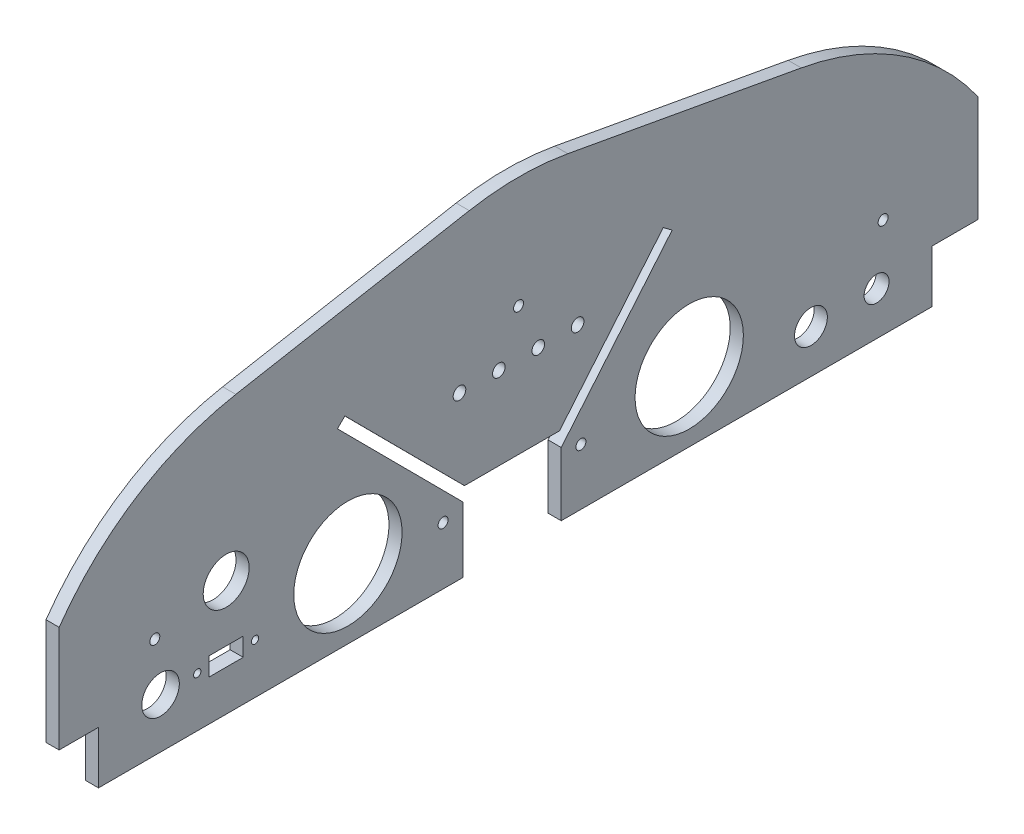
SolidWorks part; units mm, degrees
material "Maple"
ref_plane "Front Plane" through (0, 0, 0) normal (0, 0, 1) x (1, 0, 0)
ref_plane "Top Plane" through (0, 0, 0) normal (0, 1, 0) x (1, 0, 0)
ref_plane "Right Plane" through (0, 0, 0) normal (1, 0, 0) x (0, 0, -1)
sketch "Sketch1" plane through (0, 0, 0) normal (1, 0, 0) x (0, 0, -1)
  line L0 (241.201, 0) -> (185.8087, 79.3068) construction
  line L1 (241.201, 0) -> (-241.201, 0) construction
  line L2 (128.8185, 115.8696) -> (15.8924, 136.3875) construction
  line L3 (241.201, 0) -> (190.401, 0) construction
  line L4 (-15.8924, 136.3875) -> (-128.8185, 115.8696) construction
  line L5 (200.025, 53.34) -> (222.25, 53.34)
  line L6 (-185.8087, 79.3068) -> (-241.201, 0) construction
  line L7 (-241.201, 0) -> (-190.401, 0) construction
  line L8 (136.7647, 159.6035) -> (23.8385, 180.1215)
  line L9 (-137.7917, 27.94) -> (137.7917, 27.94) construction
  line L10 (-23.8385, 180.1215) -> (-136.7647, 159.6035)
  line L11 (-203.2, 53.34) -> (-222.25, 53.34)
  line L12 (222.25, 53.34) -> (222.25, 104.7594)
  line L13 (-222.25, 53.34) -> (-222.25, 104.7594)
  line L15 (200.025, 53.34) -> (200.025, 27.94)
  line L16 (200.025, 27.94) -> (-203.2, 27.94)
  line L17 (-203.2, 27.94) -> (-203.2, 53.34)
  line L18 (171.1515, 182.2695) -> (-131.8993, 182.2695) construction
  line L19 (277.6423, 25.4526) -> (222.25, 104.7594) construction
  line L20 (-222.25, 104.7594) -> (-277.6423, 25.4526) construction
  arc A0 (185.8087, 79.3068) -> (128.8185, 115.8696) centre (112.9261, 28.4016) ccw construction
  arc A1 (15.8924, 136.3875) -> (-15.8924, 136.3875) centre (0, 48.9195) ccw construction
  arc A2 (-128.8185, 115.8696) -> (-185.8087, 79.3068) centre (-112.9261, 28.4016) ccw construction
  arc A3 (-190.401, 0) -> (-137.7917, 27.94) centre (-137.7917, -35.56) cw construction
  arc A4 (137.7917, 27.94) -> (190.401, 0) centre (137.7917, -35.56) cw construction
  arc A5 (222.25, 104.7594) -> (136.7647, 159.6035) centre (112.9261, 28.4016) ccw
  arc A6 (23.8385, 180.1215) -> (-23.8385, 180.1215) centre (0, 48.9195) ccw
  arc A7 (-136.7647, 159.6035) -> (-222.25, 104.7594) centre (-112.9261, 28.4016) ccw
  point P22 (0, 27.94)
  dimension "D1" = 88.9
  dimension "D2" = 88.9
  dimension "D3" = 137.8195
  dimension "D8" = 63.5
  dimension "D4" = 114.775
  dimension "D5" = 114.775
  dimension "D6" = 257.637
  dimension "D7" = 444.5
  dimension "D9" = 27.94
  dimension "D10" = 50.8
  dimension "D12" = 25.4
  dimension "D13" = 19.05
  dimension "D14" = 22.225
  dimension "D11" = 44.45
extrude "Base" add sketch "Sketch1" along normal blind 6.35
sketch "Car Dimensions" plane through (0, 0, 0) normal (1, 0, 0) x (0, 0, -1)
  line L0 (-258.164, 20.0716) -> (-206.6323, 93.8512)
  line L2 (-133.3592, 140.8604) -> (-22.7034, 160.9658)
  line L4 (22.7034, 160.9658) -> (133.3592, 140.8604)
  line L6 (206.6323, 93.8512) -> (259.779, 17.7594)
  line L10 (228.7968, 17.7594) -> (185.8087, 79.3068)
  line L11 (131.0888, 128.365) -> (18.1627, 148.8829)
  line L13 (128.8185, 115.8696) -> (15.8924, 136.3875)
  line L14 (-18.1627, 148.8829) -> (-131.0888, 128.365)
  line L15 (-15.8924, 136.3875) -> (-128.8185, 115.8696)
  line L16 (196.2205, 86.579) -> (248.3531, 11.9391)
  line L17 (-185.8087, 79.3068) -> (-227.1819, 20.0716)
  line L18 (-196.2205, 86.579) -> (-238.3224, 26.3004)
  line L21 (-203.2, 53.34) -> (-203.2, 27.94)
  line L22 (200.025, 53.34) -> (222.25, 53.34)
  line L23 (222.25, 53.34) -> (222.25, 104.7594)
  line L24 (136.7647, 159.6035) -> (23.8385, 180.1215)
  line L25 (-23.8385, 180.1215) -> (-136.7647, 159.6035)
  line L26 (-222.25, 104.7594) -> (-222.25, 53.34)
  line L27 (-222.25, 53.34) -> (-203.2, 53.34)
  line L28 (-203.2, 53.34) -> (-203.2, 27.94)
  line L29 (-203.2, 27.94) -> (200.025, 27.94)
  line L30 (-203.2, 27.94) -> (200.025, 27.94)
  line L31 (136.7647, 159.6035) -> (23.8385, 180.1215)
  line L32 (-23.8385, 180.1215) -> (-136.7647, 159.6035)
  line L33 (200.025, 27.94) -> (200.025, 53.34)
  line L34 (200.025, 27.94) -> (200.025, 53.34)
  arc A0 (-206.6323, 93.8512) -> (-133.3592, 140.8604) centre (-112.9261, 28.4016) cw
  arc A1 (-22.7034, 160.9658) -> (22.7034, 160.9658) centre (0, 36.0116) cw
  arc A2 (133.3592, 140.8604) -> (206.6323, 93.8512) centre (112.9261, 28.4016) cw
  circle A6 centre (0, 36.0116) radius 127
  arc A7 (185.8087, 79.3068) -> (128.8185, 115.8696) centre (112.9261, 28.4016) ccw
  arc A8 (15.8924, 136.3875) -> (-15.8924, 136.3875) centre (0, 48.9195) ccw
  arc A9 (-128.8185, 115.8696) -> (-185.8087, 79.3068) centre (-112.9261, 28.4016) ccw
  arc A12 (196.2205, 86.579) -> (131.0888, 128.365) centre (112.9261, 28.4016) ccw
  arc A13 (18.1627, 148.8829) -> (-18.1627, 148.8829) centre (0, 48.9195) ccw
  arc A14 (-131.0888, 128.365) -> (-196.2205, 86.579) centre (-112.9261, 28.4016) ccw
  arc A17 (222.25, 104.7594) -> (136.7647, 159.6035) centre (112.9261, 28.4016) ccw
  arc A18 (23.8385, 180.1215) -> (-23.8385, 180.1215) centre (0, 48.9195) ccw
  arc A19 (-136.7647, 159.6035) -> (-222.25, 104.7594) centre (-112.9261, 28.4016) ccw
  arc A22 (222.25, 104.7594) -> (136.7647, 159.6035) centre (112.9261, 28.4016) ccw
  arc A23 (23.8385, 180.1215) -> (-23.8385, 180.1215) centre (0, 48.9195) ccw
  arc A24 (-136.7647, 159.6035) -> (-222.25, 104.7594) centre (-112.9261, 28.4016) ccw
  dimension "D2" = 254
  dimension "D3" = 12.7
  dimension "D1" = 12.7
  dimension "D4" = 0
  dimension "D5" = 31.75
sketch "Sketch5" plane through (0, 0, 0) normal (-1, 0, 0) x (0, 0, 1)
  line L0 (-17.4625, 27.94) -> (20.6375, 27.94) construction
  line L1 (-200.025, 27.94) -> (203.2, 27.94) construction
  line L2 (-17.4625, 27.94) -> (-17.4625, 46.99) construction
  line L3 (20.6375, 27.94) -> (20.6375, 46.99) construction
  line L4 (20.6375, 46.99) -> (95.25, 121.9687) construction
  line L5 (-17.4625, 46.99) -> (-76.2, 125.43) construction
  line L6 (-76.2, 125.43) -> (-68.5757, 131.1392) construction
  line L7 (95.25, 121.9687) -> (88.4983, 128.6874) construction
  line L8 (88.4983, 128.6874) -> (26.1569, 66.04) construction
  line L9 (23.8385, 180.1215) -> (136.7647, 159.6035) construction
  line L10 (-68.5757, 131.1392) -> (-19.828, 66.04) construction
  line L11 (-136.7647, 159.6035) -> (-23.8385, 180.1215) construction
  line L12 (23.8385, 180.1215) -> (136.7647, 159.6035) construction
  line L13 (-19.828, 66.04) -> (26.1569, 66.04) construction
  line L14 (-136.7647, 159.6035) -> (-23.8385, 180.1215) construction
  line L15 (-128.8185, 115.8696) -> (-15.8924, 136.3875) construction
  line L16 (15.8924, 136.3875) -> (128.8185, 115.8696) construction
  line L17 (-511.4071, 240.1453) -> (-231.4071, 240.1453) construction
  line L18 (-19.828, 66.04) -> (-69.9993, 126.1067)
  line L19 (-74.2969, 122.8886) -> (-69.9993, 126.1067)
  line L20 (-74.2969, 122.8886) -> (-20.6375, 58.6458)
  line L21 (-20.6375, 58.6458) -> (-20.6375, 27.94)
  line L22 (26.9875, 27.94) -> (26.9875, 59.6728)
  line L23 (84.0192, 124.1863) -> (87.6201, 120.603)
  line L24 (26.1569, 66.04) -> (84.0192, 124.1863)
  line L25 (87.6201, 120.603) -> (26.9875, 59.6728)
  line L26 (-19.828, 66.04) -> (26.1569, 66.04)
  arc A3 (23.8385, 180.1215) -> (-23.8385, 180.1215) centre (0, 48.9195) ccw construction
  arc A4 (23.8385, 180.1215) -> (-23.8385, 180.1215) centre (0, 48.9195) ccw construction
  arc A5 (15.8924, 136.3875) -> (-15.8924, 136.3875) centre (0, 48.9195) ccw construction
  point P4 (1.5875, 27.94)
  point P22 (0, 137.8195)
  dimension "D8" = 76.2
  dimension "D1" = 38.1
  dimension "D2" = 38.1
  dimension "D3" = 19.05
  dimension "D4" = 44.45
  dimension "D5" = 95.25
  dimension "D6" = 9.525
  dimension "D7" = 3.175
  dimension "D9" = 9.525
  dimension "D10" = 6.35
  dimension "D11" = 3.175
  dimension "D12" = 4.445
  dimension "D13" = 6.35
  dimension "D14" = 4.445
extrude "Steering Slot" cut sketch "Sketch5" against normal up to next
sketch "Sketch6" plane through (0, 0, 0) normal (-1, 0, 0) x (0, 0, 1)
  line L4 (-222.25, 53.34) -> (-222.25, 104.7594) construction
  line L5 (222.25, 53.34) -> (222.25, 104.7594) construction
  circle A0 centre (-82.55, 61.6195) radius 26.1938
  circle A1 centre (82.55, 61.6195) radius 26.1938
  circle A2 centre (-82.55, 61.6195) radius 28.829 construction
  circle A3 centre (82.55, 61.6195) radius 28.829 construction
  arc A4 (23.8385, 180.1215) -> (-23.8385, 180.1215) centre (0, 48.9195) ccw construction
  point P4 (0, 182.2695)
  dimension "D1" = 57.658
  dimension "D2" = 52.3875
  dimension "D3" = 120.65
  dimension "D4" = 139.7
  dimension "D5" = 139.7
extrude "Gauge Holes" cut sketch "Sketch6" against normal up to next
sketch "Sketch7" plane through (0, 0, 0) normal (-1, 0, 0) x (0, 0, 1)
  circle A0 centre (-28.575, 106.0695) radius 3.048
  circle A1 centre (-9.525, 106.0695) radius 3.048
  circle A2 centre (9.525, 106.0695) radius 3.048
  circle A3 centre (28.575, 106.0695) radius 3.048
  arc A5 (23.8385, 180.1215) -> (-23.8385, 180.1215) centre (0, 48.9195) ccw construction
  point P8 (0, 182.2695)
  point P13 (0, 182.2695)
  dimension "D1" = 76.2
  dimension "D2" = 9.525
  dimension "D4" = 6.096
  dimension "D5" = 19.05
  dimension "D6" = 19.05
  dimension "D7" = 19.05
extrude "LED Holes" cut sketch "Sketch7" against normal up to next
sketch "Sketch8" plane through (0, 0, 0) normal (-1, 0, 0) x (0, 0, 1)
  line L1 (-222.25, 53.34) -> (-222.25, 104.7594) construction
  circle A0 centre (-173.1894, 48.9195) radius 6.0325
  circle A1 centre (-141.4394, 48.9195) radius 7.9375
  arc A2 (23.8385, 180.1215) -> (-23.8385, 180.1215) centre (0, 48.9195) ccw construction
  point P4 (0, 182.2695)
  dimension "D1" = 15.875
  dimension "D2" = 12.065
  dimension "D4" = 49.0606
  dimension "D5" = 133.35
  dimension "D3" = 31.75
extrude "Buttons and Switches" cut sketch "Sketch8" against normal up to next
sketch "Logo" plane through (0, 0, 0) normal (-1, 0, 0) x (0, 0, 1)
  text T0 "Y" font "Times New Roman" height in points 72
  text T1 "Bulldogs Racing " font "Times New Roman" height in points 24
sketch "Sketch12" plane through (0, 0, 0) normal (-1, 0, 0) x (0, 0, 1)
  line L1 (133.1844, 56.5395) -> (149.6944, 47.6495) construction
  line L3 (133.1844, 56.5395) -> (149.6944, 56.5395)
  line L10 (133.1844, 56.5395) -> (133.1844, 47.6495)
  line L11 (133.1844, 47.6495) -> (149.6944, 47.6495)
  line L12 (149.6944, 56.5395) -> (149.6944, 47.6495)
  line L13 (155.4094, 52.0945) -> (127.4694, 52.0945) construction
  circle A1 centre (173.1894, 52.0945) radius 9.0805
  circle A2 centre (127.4694, 52.0945) radius 1.778
  circle A3 centre (155.4094, 52.0945) radius 1.778
  arc A4 (23.8385, 180.1215) -> (-23.8385, 180.1215) centre (0, 48.9195) ccw construction
  circle A5 centre (141.4394, 83.8445) radius 11.1125
  circle A6 centre (141.4394, 83.8445) radius 19.8755 construction
  point P3 (0, 182.2695)
  point P11 (0, 182.2695)
  point P20 (141.4394, 52.0945)
  dimension "D4" = 31.75
  dimension "D5" = 173.1894
  dimension "D11" = 3.556
  dimension "D6" = 22.225
  dimension "D7" = 39.751
  dimension "D14" = 18.161
  dimension "D8" = 16.51
  dimension "D9" = 8.89
  dimension "D10" = 31.75
  dimension "D12" = 27.94
  dimension "D13" = 98.425
extrude "Connectors" cut sketch "Sketch12" against normal through all
sketch "Sketch4" plane through (0, 0, 0) normal (-1, 0, 0) x (0, 0, 1)
  line L0 (87.6201, 120.603) -> (26.9875, 59.6728) construction
  line L1 (-74.2969, 122.8886) -> (-20.6375, 58.6458) construction
  line L2 (203.2, 53.34) -> (203.2, 27.94) construction
  line L3 (26.9875, 27.94) -> (26.9875, 59.6728) construction
  line L4 (-20.6375, 58.6458) -> (-20.6375, 27.94) construction
  line L8 (-200.025, 27.94) -> (-200.025, 53.34) construction
  line L9 (258.164, 20.0716) -> (206.6323, 93.8512) construction
  line L10 (133.3592, 140.8604) -> (22.7034, 160.9658) construction
  line L11 (-22.7034, 160.9658) -> (-133.3592, 140.8604) construction
  line L12 (-206.6323, 93.8512) -> (-259.779, 17.7594) construction
  line L13 (-228.7968, 17.7594) -> (-185.8087, 79.3068) construction
  line L14 (-128.8185, 115.8696) -> (-15.8924, 136.3875) construction
  line L15 (15.8924, 136.3875) -> (128.8185, 115.8696) construction
  line L16 (185.8087, 79.3068) -> (227.1819, 20.0716) construction
  line L17 (23.8385, 180.1215) -> (136.7647, 159.6035) construction
  line L18 (-136.7647, 159.6035) -> (-23.8385, 180.1215) construction
  line L23 (203.2, 53.34) -> (203.2, 27.94) construction
  line L25 (-200.025, 27.94) -> (-200.025, 53.34) construction
  line L26 (258.164, 20.0716) -> (206.6323, 93.8512) construction
  line L27 (133.3592, 140.8604) -> (22.7034, 160.9658) construction
  line L28 (-22.7034, 160.9658) -> (-133.3592, 140.8604) construction
  line L29 (-206.6323, 93.8512) -> (-259.779, 17.7594) construction
  line L30 (-228.7968, 17.7594) -> (-185.8087, 79.3068) construction
  line L31 (-128.8185, 115.8696) -> (-15.8924, 136.3875) construction
  line L32 (15.8924, 136.3875) -> (128.8185, 115.8696) construction
  line L33 (185.8087, 79.3068) -> (227.1819, 20.0716) construction
  line L34 (23.8385, 180.1215) -> (136.7647, 159.6035) construction
  line L35 (-136.7647, 159.6035) -> (-23.8385, 180.1215) construction
  arc A0 (206.6323, 93.8512) -> (133.3592, 140.8604) centre (112.9261, 28.4016) ccw construction
  circle A1 centre (0, 128.2945) radius 9.525 construction
  circle A2 centre (0, 128.2945) radius 2.413
  arc A3 (22.7034, 160.9658) -> (-22.7034, 160.9658) centre (0, 36.0116) ccw construction
  arc A5 (-133.3592, 140.8604) -> (-206.6323, 93.8512) centre (-112.9261, 28.4016) ccw construction
  arc A6 (-128.8185, 115.8696) -> (-185.8087, 79.3068) centre (-112.9261, 28.4016) ccw construction
  arc A8 (15.8924, 136.3875) -> (-15.8924, 136.3875) centre (0, 48.9195) ccw construction
  arc A9 (185.8087, 79.3068) -> (128.8185, 115.8696) centre (112.9261, 28.4016) ccw construction
  arc A10 (222.25, 104.7594) -> (136.7647, 159.6035) centre (112.9261, 28.4016) ccw construction
  arc A11 (23.8385, 180.1215) -> (-23.8385, 180.1215) centre (0, 48.9195) ccw construction
  arc A12 (-136.7647, 159.6035) -> (-222.25, 104.7594) centre (-112.9261, 28.4016) ccw construction
  arc A16 (206.6323, 93.8512) -> (133.3592, 140.8604) centre (112.9261, 28.4016) ccw construction
  arc A17 (22.7034, 160.9658) -> (-22.7034, 160.9658) centre (0, 36.0116) ccw construction
  arc A18 (-133.3592, 140.8604) -> (-206.6323, 93.8512) centre (-112.9261, 28.4016) ccw construction
  arc A19 (-128.8185, 115.8696) -> (-185.8087, 79.3068) centre (-112.9261, 28.4016) ccw construction
  arc A20 (15.8924, 136.3875) -> (-15.8924, 136.3875) centre (0, 48.9195) ccw construction
  arc A21 (185.8087, 79.3068) -> (128.8185, 115.8696) centre (112.9261, 28.4016) ccw construction
  arc A22 (222.25, 104.7594) -> (136.7647, 159.6035) centre (112.9261, 28.4016) ccw construction
  arc A23 (23.8385, 180.1215) -> (-23.8385, 180.1215) centre (0, 48.9195) ccw construction
  arc A24 (-136.7647, 159.6035) -> (-222.25, 104.7594) centre (-112.9261, 28.4016) ccw construction
  circle A25 centre (-176.3499, 76.1281) radius 9.525 construction
  circle A26 centre (-176.3499, 76.1281) radius 2.413
  circle A27 centre (175.9555, 76.6477) radius 9.525 construction
  circle A28 centre (175.9555, 76.6477) radius 2.413
  circle A29 centre (-30.1625, 55.1912) radius 9.525 construction
  circle A30 centre (-30.1625, 55.1912) radius 2.413
  circle A31 centre (36.5125, 55.7411) radius 9.525 construction
  circle A32 centre (36.5125, 55.7411) radius 2.413
  dimension "D1" = 19.05
  dimension "D2" = 4.826
  dimension "D3" = 19.05
  dimension "D4" = 4.826
  dimension "D5" = 19.05
  dimension "D6" = 4.826
  dimension "D8" = 19.05
  dimension "D9" = 4.826
  dimension "D10" = 19.05
  dimension "D11" = 4.826
extrude "Mounting Holes" cut sketch "Sketch4" against normal up to next
